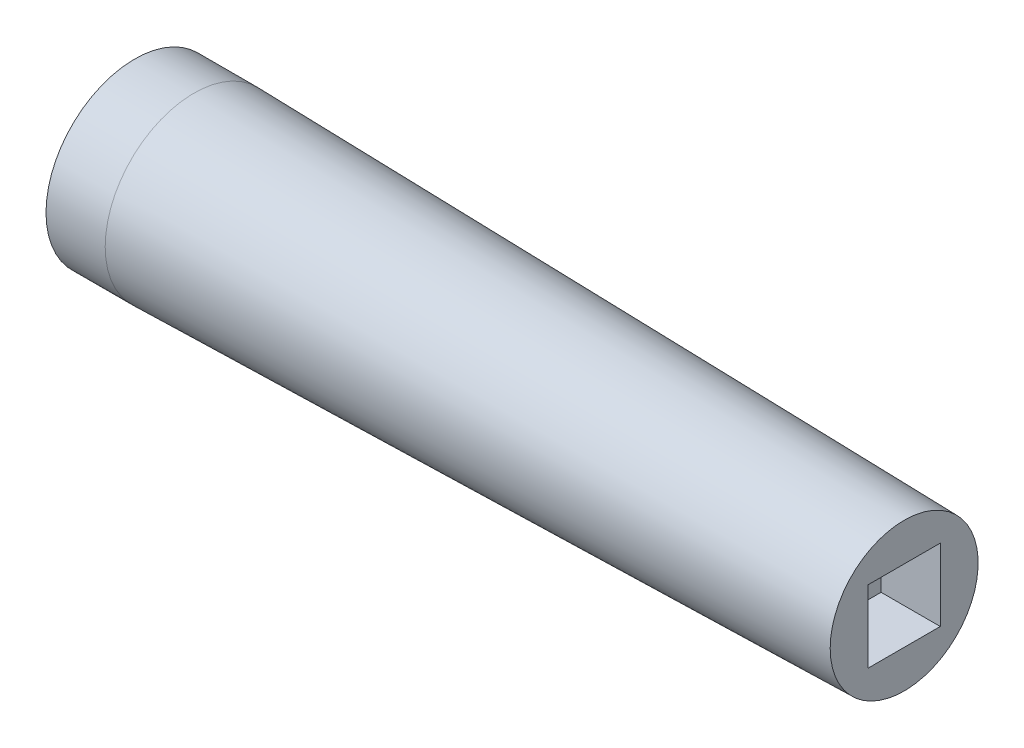
SolidWorks part; units mm, degrees
ref_plane "Front Plane" through (0, 0, 0) normal (0, 0, 1) x (1, 0, 0)
ref_plane "Top Plane" through (0, 0, 0) normal (0, 1, 0) x (1, 0, 0)
ref_plane "Right Plane" through (0, 0, 0) normal (1, 0, 0) x (0, 0, -1)
sketch "Sketch2" plane through (0, 0, 0) normal (0, 0, 1) x (1, 0, 0)
  line L0 (-5.7379, 0) -> (4.6445, 0) construction
  line L1 (0, 0) -> (0, 19.05)
  line L2 (0, 19.05) -> (12.7, 19.05)
  line L3 (12.7, 19.05) -> (165.1, 15.875)
  line L4 (165.1, 15.875) -> (165.1, 0)
  line L5 (165.1, 0) -> (0, 0)
  dimension "D1" = 165.1
  dimension "D2" = 12.7
  dimension "D3" = 38.1
  dimension "D4" = 31.75
revolve "Revolve5" add sketch "Sketch2" angle 360 about L0
sketch "Sketch3" plane through (165.1, 0, 0) normal (1, 0, 0) x (0, 0, -1)
  line L0 (0, 19.05) -> (0, -19.05) construction
  line L1 (-19.05, 0) -> (19.05, 0) construction
  line L3 (7.747, -7.747) -> (-7.747, -7.747)
  line L4 (7.747, -7.747) -> (7.747, 7.747)
  line L5 (7.747, 7.747) -> (-7.747, 7.747)
  line L6 (-7.747, -7.747) -> (-7.747, 7.747)
  line L7 (7.747, -7.747) -> (-7.747, 7.747) construction
  line L8 (7.747, 7.747) -> (-7.747, -7.747) construction
  circle A0 centre (0, 0) radius 19.05 construction
  point P8 (0, 0)
  dimension "D1" = 15.494
extrude "Cut-Extrude1" cut sketch "Sketch3" against normal blind 12.7
